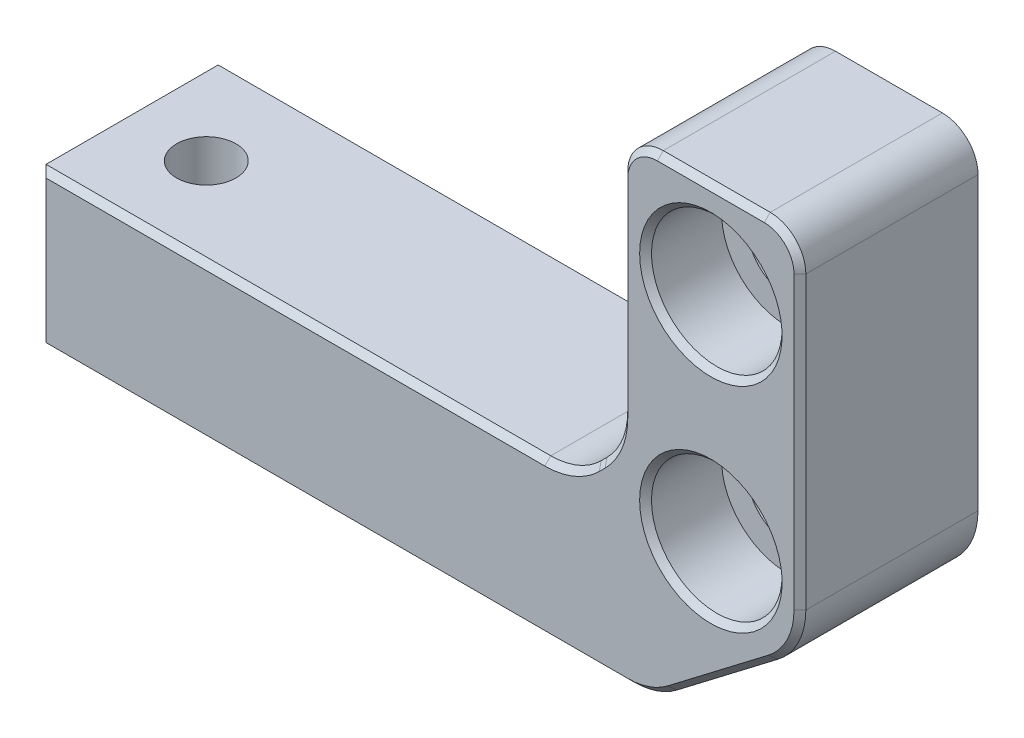
SolidWorks part; units mm, degrees
material "Alumina"
ref_plane "Plan de face" through (0, 0, 0) normal (0, 0, 1) x (1, 0, 0)
ref_plane "Plan de dessus" through (0, 0, 0) normal (0, 1, 0) x (1, 0, 0)
ref_plane "Plan de droite" through (0, 0, 0) normal (1, 0, 0) x (0, 0, -1)
sketch "Sketch1" plane through (0, 0, 0) normal (0, 0, 1) x (1, 0, 0)
  line L0 (26, 20.7005) -> (26, -11.3325) construction
  line L1 (22.6582, -18.5995) -> (31.1435, -12.1143)
  line L2 (16.2574, -5.0751) -> (16.7426, -4.5898)
  line L3 (-25, 4.1675) -> (-25, 20.7005) construction
  line L4 (-30.5, -6.8325) -> (12.0147, -6.8325)
  line L5 (-30.5, -6.8325) -> (-30.5, -19.8325)
  line L6 (-30.5, -19.8325) -> (19.0147, -19.8325)
  line L7 (33.5, -7.3472) -> (33.5, 17.1675)
  line L8 (30.5, 20.1675) -> (21.5, 20.1675)
  line L9 (18.5, -0.3472) -> (18.5, 17.1675)
  arc A0 (21.5, 20.1675) -> (18.5, 17.1675) centre (21.5, 17.1675) ccw
  arc A1 (33.5, 17.1675) -> (30.5, 20.1675) centre (30.5, 17.1675) ccw
  arc A2 (22.6582, -18.5995) -> (19.0147, -19.8325) centre (19.0147, -13.8325) cw
  arc A3 (31.1435, -12.1143) -> (33.5, -7.3472) centre (27.5, -7.3472) ccw
  arc A4 (16.2574, -5.0751) -> (12.0147, -6.8325) centre (12.0147, -0.8325) cw
  arc A5 (16.7426, -4.5898) -> (18.5, -0.3472) centre (12.5, -0.3472) ccw
  point P1 (33.5, -19.8325)
  point P7 (18.5, -6.8325)
  point P26 (0, 0)
  point P27 (0, 0)
  dimension "D2" = 3
  dimension "D3" = 6
  dimension "D1" = 5.5
  dimension "D4" = 40
  dimension "D5" = 13
  dimension "D6" = 15
  dimension "D7" = 7.5
extrude "Boss-Extrude1" add sketch "Sketch1" along normal blind 15
hole_wizard "CBORE for M6 Hex Socket Head Cap Screw1" positions "Sketch2" profile "Sketch3" counterbore size "M6" standard "ISO" end condition through all
sketch "Sketch2" plane through (0, 0, 15) normal (0, 0, 1) x (1, 0, 0)
  line L0 (30.5, 20.1675) -> (21.5, 20.1675) construction
  point P0 (26, 12.1675)
  point P2 (26, -5.8325)
  point P5 (0, 0)
  point P6 (26, 20.1675)
  dimension "D1" = 18
  dimension "D2" = 8
sketch "Sketch3" plane through (26, 12.1675, 15) normal (1, 0, 0) x (0, -1, 0)
  line L0 (0, 0) -> (0, 15)
  line L1 (0, 15) -> (3.3, 15)
  line L3 (3.3, 15) -> (3.3, 6.4)
  line L4 (3.3, 6.4) -> (5.5, 6.4)
  line L5 (5.5, 6.4) -> (5.5, 0)
  line L7 (5.5, 0) -> (0, 0)
  line L11 (0, -6.35) -> (0, 107.95) construction
  dimension "Thru Hole Dia." = 6.6
  dimension "Thru Hole Depth" = 15
  dimension "C'Bore Dia." = 11
  dimension "C'Bore Depth" = 6.4
hole_wizard "Tap Drill for M6 Tap1" positions "Sketch4" profile "Sketch5" hole size "M6" standard "ISO" end condition through all
sketch "Sketch4" plane through (0, -6.8325, 0) normal (0, 1, 0) x (1, 0, 0)
  line L0 (-30.5, -15) -> (-30.5, 0) construction
  point P0 (-24, -7.5)
  dimension "D1" = 6.5
sketch "Sketch5" plane through (-24, -6.8325, 7.5) normal (1, 0, 0) x (0, 0, 1)
  line L0 (0, 0) -> (0, 13)
  line L1 (0, 13) -> (2.5, 13)
  line L2 (2.5, 13) -> (2.5, 0)
  line L5 (2.5, 0) -> (0, 0)
  line L11 (0, -6.35) -> (0, 107.95) construction
  dimension "Thru Hole Dia." = 5
  dimension "Thru Hole Depth" = 13
chamfer "Chamfer1" distance 0.5 angle 45 16 edges at (31.5, 12.1675, 15) (31.5, -5.8325, 15) (-5.7426, -19.8325, 15) (20.9379, -19.5159, 15) (26.9008, -15.3569, 15) (32.8787, -10.006, 15) (33.5, 4.9102, 15) (32.6213, 19.2889, 15) (26, 20.1675, 15) (19.3787, 19.2889, 15) (18.5, 8.4102, 15) (18.0433, -2.6433, 15) (16.5, -4.8325, 15) (14.3108, -6.3757, 15) (-30.5, -13.3325, 15) (-9.2426, -6.8325, 15)
